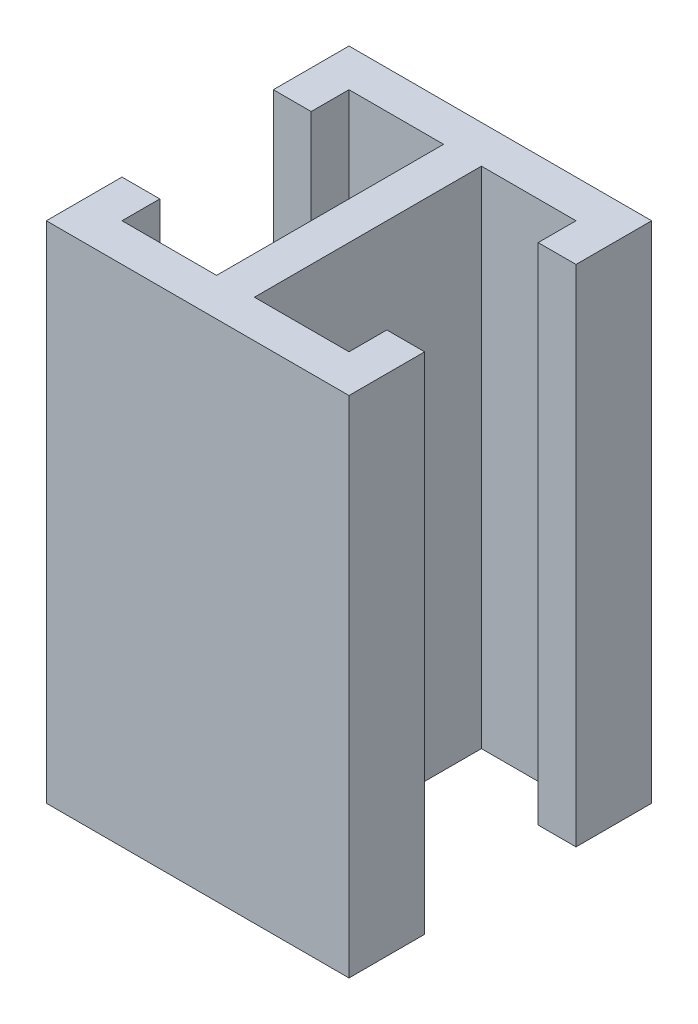
SolidWorks part; units mm, degrees
ref_plane "正面" through (0, 0, 0) normal (0, 0, 1) x (1, 0, 0)
ref_plane "平面" through (0, 0, 0) normal (0, 1, 0) x (1, 0, 0)
ref_plane "右側面" through (0, 0, 0) normal (1, 0, 0) x (0, 0, -1)
sketch "ｽｹｯﾁ5" plane through (0, 0, 0) normal (0, 1, 0) x (1, 0, 0)
  line L1 (0, 0) -> (120, 0)
  line L2 (0, 0) -> (0, 30)
  line L3 (0, 120) -> (120, 120)
  line L4 (120, 0) -> (120, 30)
  line L6 (52.5, 105) -> (15, 105)
  line L7 (52.5, 105) -> (52.5, 15)
  line L8 (52.5, 15) -> (15, 15)
  line L9 (15, 105) -> (15, 90)
  line L11 (15, 90) -> (0, 90)
  line L13 (15, 30) -> (0, 30)
  line L16 (67.5, 105) -> (105, 105)
  line L17 (67.5, 105) -> (67.5, 15)
  line L18 (67.5, 15) -> (105, 15)
  line L19 (105, 105) -> (105, 90)
  line L20 (0, 90) -> (0, 120)
  line L21 (105, 90) -> (120, 90)
  line L23 (105, 30) -> (120, 30)
  line L25 (15, 30) -> (15, 15)
  line L26 (120, 90) -> (120, 120)
  line L27 (105, 30) -> (105, 15)
  point P0 (0, 0)
  point P1 (0, 30)
  point P2 (15.8065, 48.2826)
  point P3 (15, 15)
  point P5 (64.9248, 14.7929)
  point P6 (52.5, 105)
  point P7 (15.8065, 137.9607)
  point P8 (15, 90)
  point P9 (0, 108.5641)
  point P10 (0, 155.4498)
  point P11 (120, 120)
  point P12 (136.7417, 108.5641)
  point P13 (105, 90)
  point P14 (118.8805, 137.9607)
  point P15 (67.5, 105)
  point P16 (84.2744, 14.7929)
  point P17 (105, 15)
  point P18 (118.8805, 48.2826)
  point P19 (120, 30)
  point P20 (136.7417, 0)
  dimension "D1" = 120
  dimension "D2" = 15
  dimension "D3" = 15
  dimension "D4" = 120
  dimension "D5" = 15
  dimension "D6" = 15
  dimension "D7" = 15
  dimension "D8" = 15
  dimension "D9" = 15
  dimension "D10" = 52.5
  dimension "D11" = 30
  dimension "D12" = 30
  dimension "D13" = 30
  dimension "D14" = 30
extrude "ﾎﾞｽ - 押し出し1" add sketch "ｽｹｯﾁ5" along normal blind 200
fillet "ﾌｨﾚｯﾄ1" [suppressed] radius 22.5
fillet "ﾌｨﾚｯﾄ2" [suppressed] radius 7.5
equation "\"C\" = 30"
equation "\"B\"= 15"
equation "\"A\"= 15"
equation "\"D2@ｽｹｯﾁ5\"=\"B\""
equation "\"D3@ｽｹｯﾁ5\"=\"B\""
equation "\"D5@ｽｹｯﾁ5\"=\"B\""
equation "\"D6@ｽｹｯﾁ5\"=\"B\""
equation "\"D7@ｽｹｯﾁ5\"=\"B\""
equation "\"D8@ｽｹｯﾁ5\"=\"B\""
equation "\"D9@ｽｹｯﾁ5\"=\"A\""
equation "\"D11@ｽｹｯﾁ5\"=\"C\""
equation "\"D12@ｽｹｯﾁ5\"=\"C\""
equation "\"D13@ｽｹｯﾁ5\"=\"C\""
equation "\"D14@ｽｹｯﾁ5\"=\"C\""
equation "\"D10@ｽｹｯﾁ5\"=60 - \"A\"/2"
equation "\"D1@ﾌｨﾚｯﾄ1\"=\"B\"/2*3"
equation "\"D1@ﾌｨﾚｯﾄ2\"=\"B\"/2"
equation "\"D\"= IIF ( INT ( 1 ) = 1 , COS ( 0 ) , sIn ( 0 ) )"
equation "\"E\" = 10cm"
